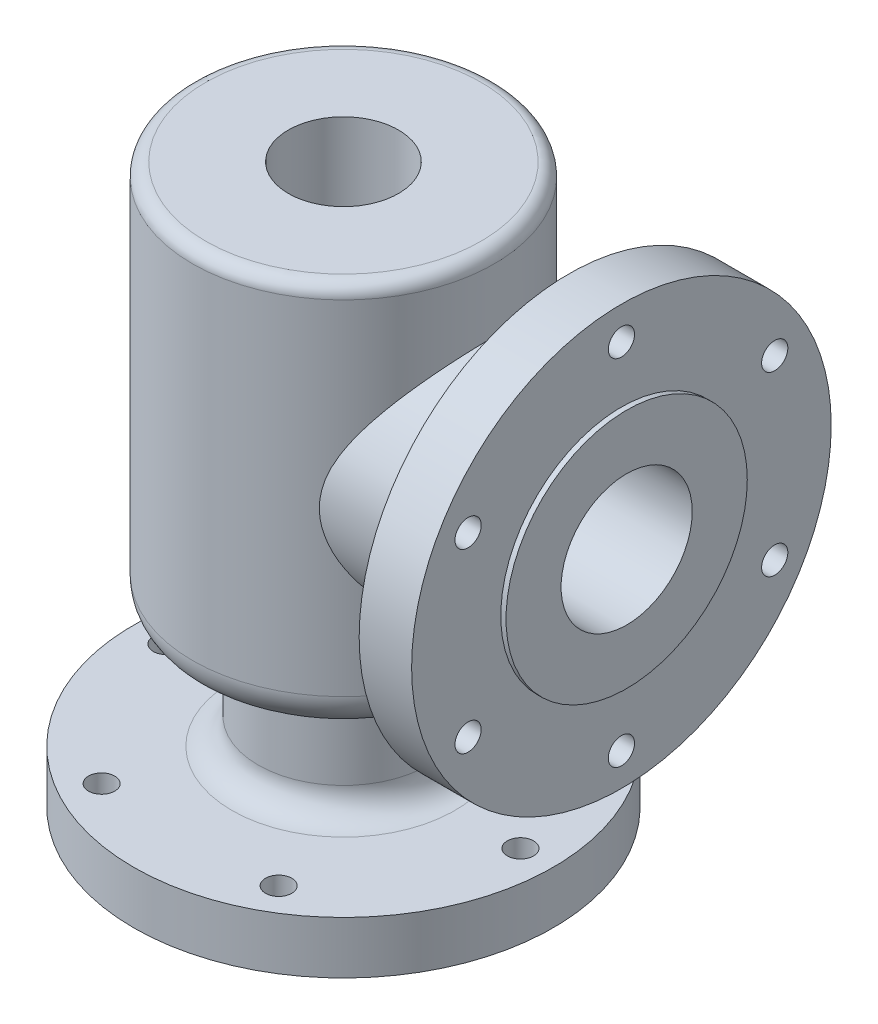
SolidWorks part; units mm, degrees
ref_plane "Přední rovina" through (0, 0, 0) normal (0, 0, 1) x (1, 0, 0)
ref_plane "Vrchní rovina" through (0, 0, 0) normal (0, 1, 0) x (1, 0, 0)
ref_plane "Pravá rovina" through (0, 0, 0) normal (1, 0, 0) x (0, 0, -1)
sketch "Skica1" plane through (0, 0, 0) normal (0, 0, 1) x (1, 0, 0)
  line L0 (0, 44.7321) -> (0, -356.1278) construction
  line L1 (0, 0) -> (57.5, 0)
  line L2 (57.5, 0) -> (57.5, -150)
  line L3 (57.5, -150) -> (32.5, -150)
  line L4 (32.5, -150) -> (32.5, -193)
  line L5 (32.5, -193) -> (80, -193)
  line L6 (80, -193) -> (80, -213)
  line L7 (45, -215) -> (12.5, -215)
  line L8 (80, -213) -> (45, -213)
  line L9 (45, -213) -> (45, -215)
  line L10 (21, 0) -> (21, -30)
  line L11 (21, -30) -> (43, -30)
  line L12 (43, -30) -> (43, -118)
  line L13 (43, -118) -> (12.5, -118)
  line L15 (12.5, -118) -> (12.5, -215)
  dimension "D1" = 215
  dimension "D2" = 150
  dimension "D3" = 90
  dimension "D4" = 160
  dimension "D5" = 65
  dimension "D6" = 115
  dimension "D7" = 20
  dimension "D8" = 2
  dimension "D9" = 30
  dimension "D10" = 25
  dimension "D11" = 86
  dimension "D12" = 42
  dimension "D13" = 88
revolve "Rotovat1" add sketch "Skica1" angle 360 about L0
fillet "Zaoblit1" radius 10 4 edges at (0, -193, 32.5) (0, -150, 32.5) (0, -118, 43) (0, -30, 43)
fillet "Zaoblit2" radius 14 1 edges at (0, -150, 57.5)
chamfer "Zkosení1" distance 8 angle 45 1 edges at (0, -118, 12.5)
fillet "Zaoblit3" radius 5 1 edges at (0, 0, 57.5)
sketch "Skica3" plane through (0, -213, 0) normal (0, -1, 0) x (1, 0, 0)
  line L0 (0, 0) -> (92.6808, 0) construction
  circle A0 centre (67.5, 0) radius 5
  circle A6 centre (0, 0) radius 67.5 construction
  point P22 (0, 0)
  dimension "D2" = 10
  dimension "D1" = 135
extrude "Odebrat vysunutím3" cut sketch "Skica3" against normal up to next (20 mm away)
pattern_circular "Kruhové pole1" count 6 over 360 about axis through (0, 0, 0) along (0, 1, 0) of "Odebrat vysunutím3"
ref_plane "Rovina1" through (86, 0, 0) normal (1, 0, 0) x (0, 0, -1)
sketch "Skica4" plane through (86, 0, 0) normal (1, 0, 0) x (0, 0, -1)
  line L0 (52.5, 0) -> (-52.5, 0) construction
  circle A0 centre (0, -74) radius 45
  dimension "D1" = 90
  dimension "D2" = 74
extrude "Přidat vysunutím2" add sketch "Skica4" against normal up to surface (50.2054 mm away) contours A0
sketch "Skica5" plane through (86, 0, 0) normal (1, 0, 0) x (0, 0, -1)
  circle A0 centre (0, -74) radius 80
  dimension "D1" = 160
extrude "Přidat vysunutím3" add sketch "Skica5" along normal blind 20
sketch "Skica6" plane through (106, 0, 0) normal (1, 0, 0) x (0, 0, -1)
  line L0 (-80, -74) -> (80, -74) construction
  line L1 (0, 6) -> (0, -154) construction
  circle A0 centre (0, -74) radius 80 construction
  circle A1 centre (0, -74) radius 46
  dimension "D1" = 92
extrude "Přidat vysunutím4" add sketch "Skica6" along normal blind 2
sketch "Skica7" plane through (108, 0, 0) normal (1, 0, 0) x (0, 0, -1)
  circle A0 centre (0, -74) radius 25
  dimension "D1" = 50
extrude "Odebrat vysunutím4" cut sketch "Skica7" against normal up to surface (73.0143 mm away)
sketch "Skica8" plane through (106, 0, 0) normal (1, 0, 0) x (0, 0, -1)
  line L0 (0, 6) -> (0, -74) construction
  circle A0 centre (0, -74) radius 80 construction
  circle A1 centre (0, -6.5) radius 5
  circle A2 centre (0, -74) radius 67.5 construction
  dimension "D1" = 10
  dimension "D2" = 135
extrude "Odebrat vysunutím5" cut sketch "Skica8" against normal up to next (20 mm away) contours A1
pattern_circular "Kruhové pole2" count 6 over 360 about axis through (0, -74, 0) along (1, 0, 0) of "Odebrat vysunutím5"
